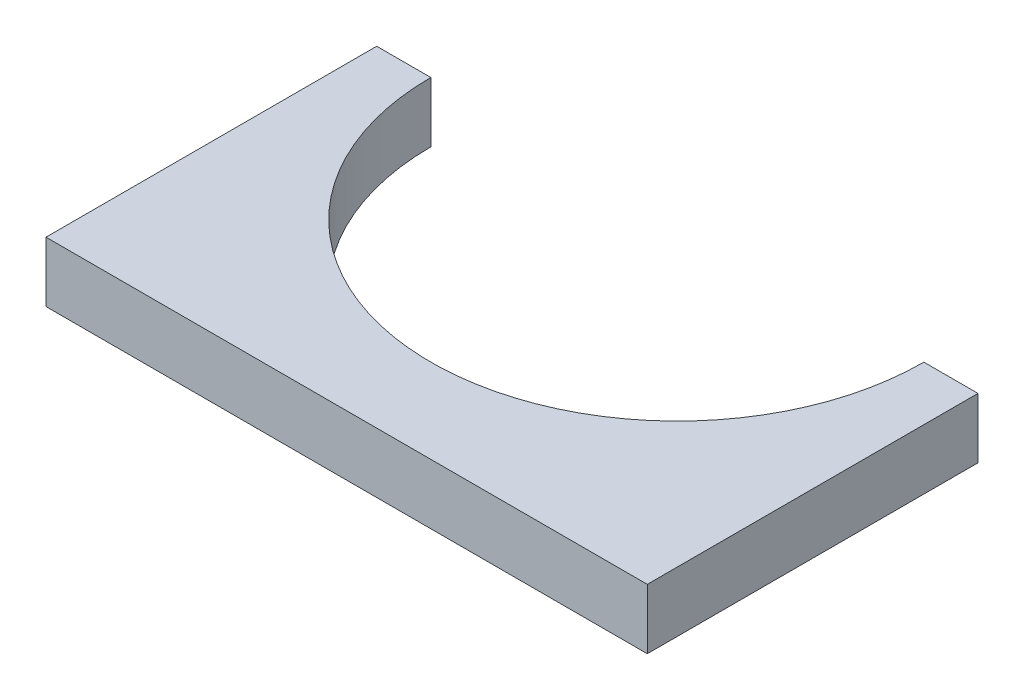
SolidWorks part; units mm, degrees
ref_plane "Спереди" through (0, 0, 0) normal (0, 0, 1) x (1, 0, 0)
ref_plane "Сверху" through (0, 0, 0) normal (0, 1, 0) x (1, 0, 0)
ref_plane "Справа" through (0, 0, 0) normal (1, 0, 0) x (0, 0, -1)
sketch "Эскиз1" plane through (0, 0, 0) normal (0, 1, 0) x (1, 0, 0)
  line L0 (-100, 0) -> (100, 0)
  line L1 (-82, 110) -> (-100, 110)
  line L2 (-100, 110) -> (-100, 0)
  line L3 (82, 110) -> (100, 110)
  line L4 (100, 110) -> (100, 0)
  arc A0 (-82, 110) -> (82, 110) centre (0, 110) ccw
  point P4 (0, 0)
extrude "Бобышка-Вытянуть1" add sketch "Эскиз1" along normal blind 20
